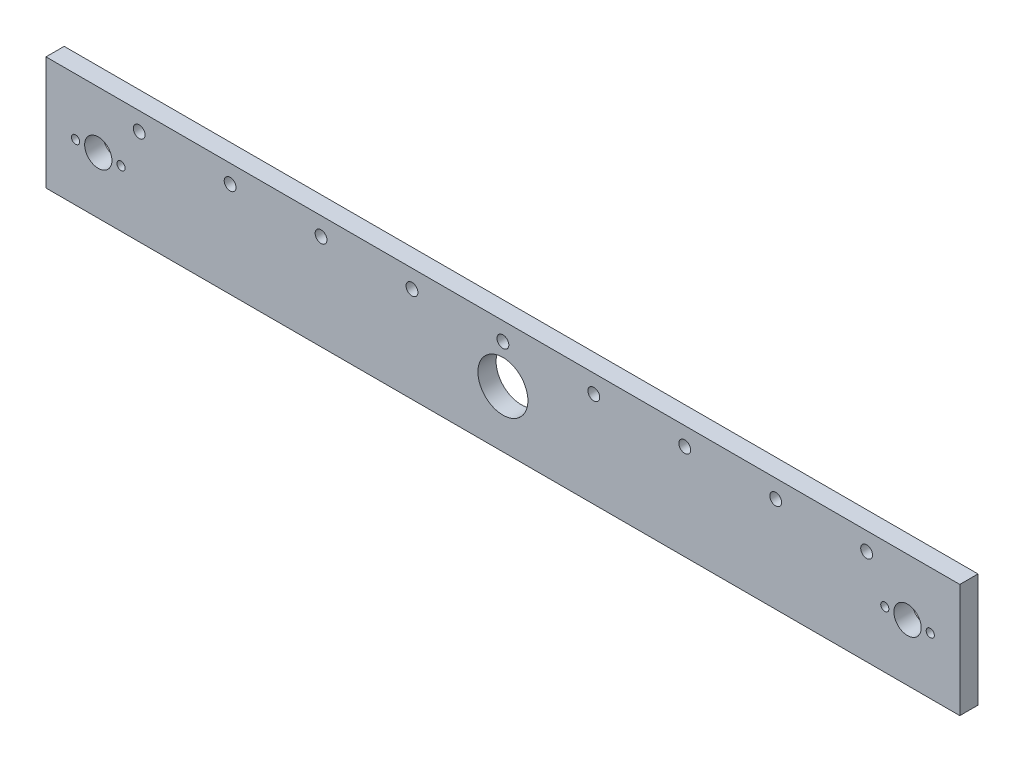
SolidWorks part; units mm, degrees
ref_plane "Front Plane" through (0, 0, 0) normal (0, 0, 1) x (1, 0, 0)
ref_plane "Top Plane" through (0, 0, 0) normal (0, 1, 0) x (1, 0, 0)
ref_plane "Right Plane" through (0, 0, 0) normal (1, 0, 0) x (0, 0, -1)
sketch "Sketch1" plane through (0, 0, 0) normal (0, 0, 1) x (1, 0, 0)
  line L0 (0, 0) -> (-200, 0) construction
  line L1 (-201, -25) -> (201, -25)
  line L2 (-201, -25) -> (-201, 25)
  line L3 (-201, 25) -> (201, 25)
  line L4 (201, -25) -> (201, 25)
  line L5 (-201, -25) -> (201, 25) construction
  line L6 (-201, 25) -> (201, -25) construction
  line L7 (0, 25) -> (0, -26) construction
  circle A0 centre (-178, 0) radius 6
  circle A1 centre (168, 0) radius 1.8
  circle A2 centre (0, 0) radius 11
  circle A3 centre (-188, 0) radius 1.8
  circle A4 centre (-168, 0) radius 1.8
  circle A5 centre (188, 0) radius 1.8
  circle A6 centre (178, 0) radius 6
  circle A7 centre (0, 17) radius 2.6
  circle A8 centre (-40, 17) radius 2.6
  circle A9 centre (-80, 17) radius 2.6
  circle A10 centre (-120, 17) radius 2.6
  circle A11 centre (-160, 17) radius 2.6
  circle A12 centre (40, 17) radius 2.6
  circle A13 centre (80, 17) radius 2.6
  circle A14 centre (120, 17) radius 2.6
  circle A15 centre (160, 17) radius 2.6
  point P0 (0, 0)
  dimension "D1" = 50
  dimension "D2" = 402
  dimension "D3" = 178
  dimension "D4" = 10
  dimension "D5" = 10
  dimension "D6" = 8
  dimension "D7" = 178
extrude "Boss-Extrude1" add sketch "Sketch1" along normal blind 8 contours L3 L4 L1 L2
